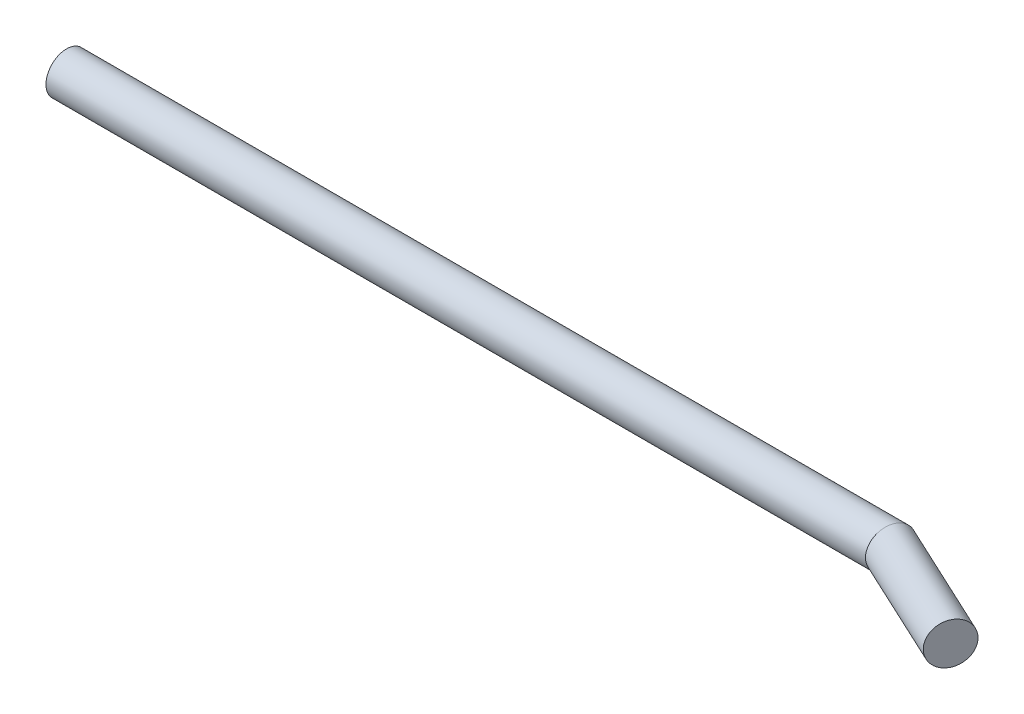
SolidWorks part; units mm, degrees
ref_plane "Alzado" through (0, 0, 0) normal (0, 0, 1) x (1, 0, 0)
ref_plane "Planta" through (0, 0, 0) normal (0, 1, 0) x (1, 0, 0)
ref_plane "Vista lateral" through (0, 0, 0) normal (1, 0, 0) x (0, 0, -1)
sketch "Croquis1" plane through (0, 0, 0) normal (0, 1, 0) x (1, 0, 0)
  line L0 (-220, 0) -> (0, 0)
  line L1 (-55, 0) -> (55, 0) construction
  line L2 (0, 0) -> (30, -13.9892)
  dimension "D1" = 250
  dimension "D2" = 25
  dimension "D3" = 30
sketch "Croquis3" plane through (0, 0, 0) normal (1, 0, 0) x (0, 0, -1)
  circle A0 centre (0, 0) radius 5.5
  dimension "D1" = 11
sweep "Barrer1" add profiles "Croquis3" path "Croquis1"
